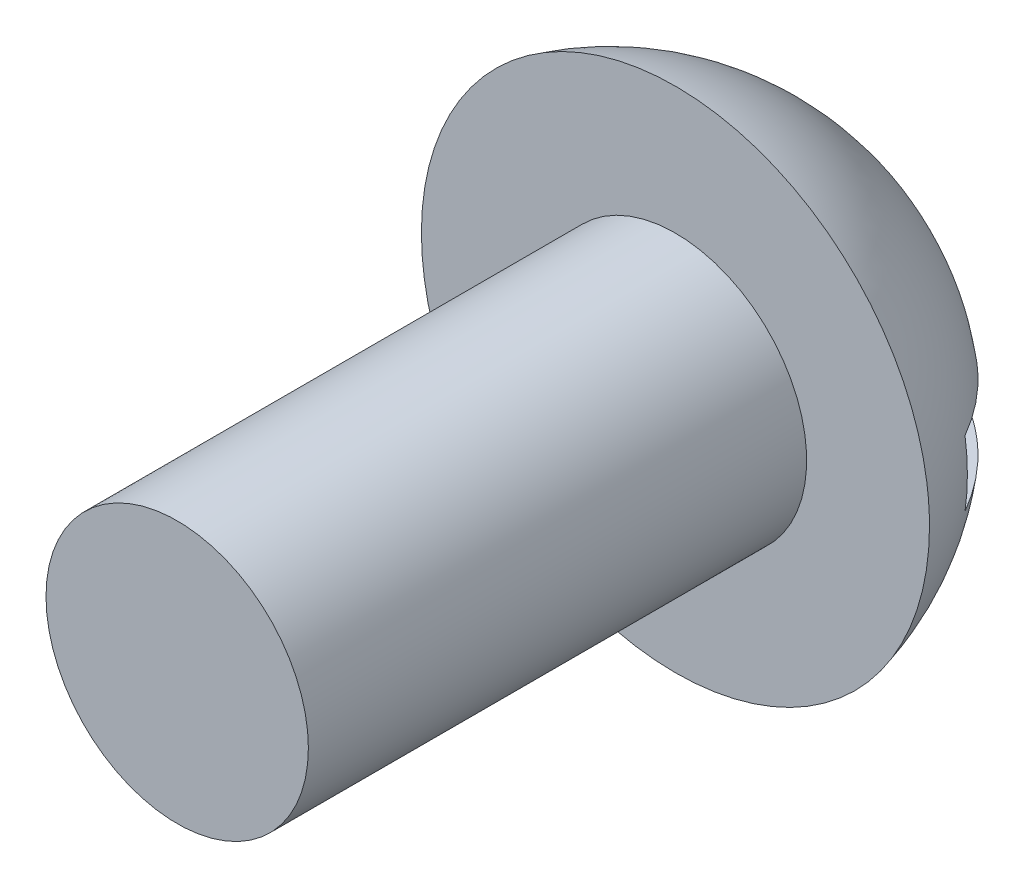
SolidWorks part; units mm, degrees
revolve "Base-Revolve" add sketch "Sketch1" angle 360 about L1
sketch "Sketch1" plane through (0, 0, 0) normal (1, 0, 0) x (0, 0, -1)
  line L0 (-22.86, 15.2822) -> (-20.974, 15.2822)
  line L1 (-28.5941, 15.2822) -> (6.9659, 15.2822) construction
  line L2 (-22.86, 17.7169) -> (-22.86, 15.2822)
  arc A0 (-20.974, 15.2822) -> (-22.86, 17.7169) centre (-23.4886, 15.2822) ccw
  dimension "D2" = 2.5146
  dimension "D1" = 1.886
ref_plane "Plane1" through (0, 0, 0) normal (0, 0, 1) x (1, 0, 0)
ref_plane "Plane2" through (0, 0, 0) normal (0, 1, 0) x (1, 0, 0)
ref_plane "Plane3" through (0, 0, 0) normal (1, 0, 0) x (0, 0, -1)
sketch "Sketch2" plane through (0, 0, 22.86) normal (0, 0, 1) x (1, 0, 0)
  circle A0 centre (0, 15.24) radius 1.2573
  dimension "D1" = 2.5146
extrude "Boss-Extrude1" add sketch "Sketch2" along normal blind 4.7752
cosmetic thread "Cosmetic Thread1" parameters "D1"=4.7752, "D2"=2.0066
sketch "Sketch4" plane through (0, 0, 0) normal (1, 0, 0) x (0, 0, -1)
  line L2 (-22.2511, 14.9678) -> (-20.9938, 14.9678)
  line L3 (-22.2511, 15.5965) -> (-20.9938, 15.5965)
  line L4 (-22.2511, 15.5965) -> (-22.2511, 14.9678)
  arc A1 (-22.86, 12.8474) -> (-22.86, 17.7169) centre (-23.4886, 15.2822) ccw construction
  arc A2 (-20.9938, 14.9678) -> (-20.9938, 15.5965) centre (-23.4886, 15.2822) ccw
  dimension "D2" = 0.6287
  dimension "D1" = 1.2573
  dimension "D3" = 0.3143
extrude "Cut-Extrude1" cut sketch "Sketch4" against normal through all
mirror "Mirror1" about plane through (0, 15.2822, 23.4886) normal (1, 0, 0) of "Cut-Extrude1"
equation "\"D1@Sketch1\"=(3/4)*\"D1@Sketch2\""
equation "\"D2@Sketch1\"=\"D1@Sketch2\""
equation "\"D1@Sketch4\"=.5*\"D1@Sketch2\""
equation "\"D2@Sketch4\"=.25*\"D1@Sketch2\""
equation "\"D3@Sketch4\"=(1/8)*\"D1@Sketch2\""
